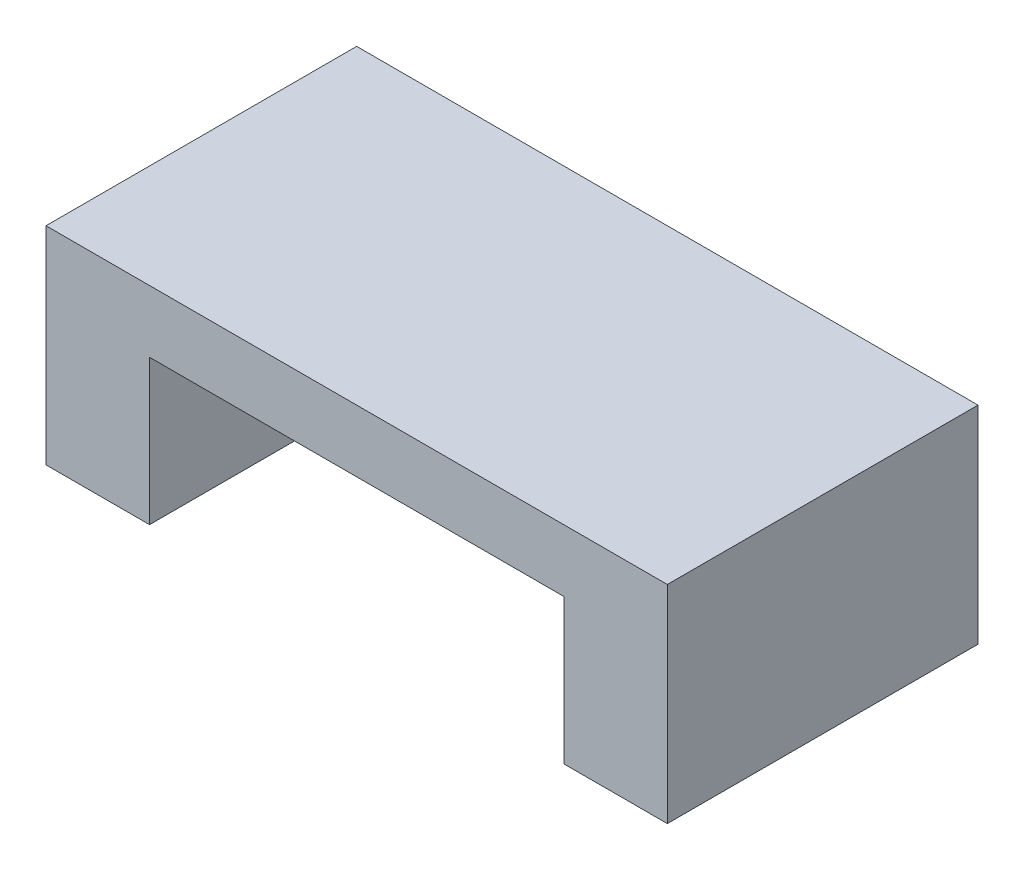
SolidWorks part; units mm, degrees
ref_plane "Front Plane" through (0, 0, 0) normal (0, 0, 1) x (1, 0, 0)
ref_plane "Top Plane" through (0, 0, 0) normal (0, 1, 0) x (1, 0, 0)
ref_plane "Right Plane" through (0, 0, 0) normal (1, 0, 0) x (0, 0, -1)
sketch "Sketch3" plane through (0, 0, 0) normal (0, 1, 0) x (1, 0, 0)
  line L1 (-15, -7.5) -> (15, -7.5)
  line L2 (-15, -7.5) -> (-15, 7.5)
  line L3 (-15, 7.5) -> (15, 7.5)
  line L4 (15, -7.5) -> (15, 7.5)
  line L5 (-15, -7.5) -> (15, 7.5) construction
  line L6 (-15, 7.5) -> (15, -7.5) construction
  point P0 (0, 0)
  dimension "D1" = 30
  dimension "D2" = 15
extrude "Boss-Extrude1" add sketch "Sketch3" along normal blind 10
sketch "Sketch4" plane through (0, 0, 7.5) normal (0, 0, 1) x (1, 0, 0)
  line L0 (-15, 0) -> (15, 0) construction
  line L1 (-10, 0) -> (10, 0)
  line L2 (-10, 0) -> (-10, 7)
  line L3 (-10, 7) -> (10, 7)
  line L4 (10, 0) -> (10, 7)
  line L5 (-15, 10) -> (-15, 0) construction
  line L6 (15, 10) -> (15, 0) construction
  dimension "D1" = 7
  dimension "D2" = 5
  dimension "D3" = 5
extrude "Cut-Extrude1" cut sketch "Sketch4" against normal through all
sketch "Sketch5" plane through (0, 0, 0) normal (0, -1, 0) x (1, 0, 0)
  line L0 (10, -7.5) -> (10, 7.5) construction
  line L1 (10, 7.5) -> (15, 7.5) construction
  line L2 (-10, -7.5) -> (-10, 7.5) construction
  line L3 (-15, 7.5) -> (-10, 7.5) construction
  circle A0 centre (12.5, 0) radius 1.5
  circle A1 centre (-12.5, 0) radius 1.5
  point P10 (0, 0)
  dimension "D1" = 2.5
  dimension "D3" = 2.5
  dimension "D2" = 7.5
  dimension "D4" = 7.5
extrude "Cut-Extrude2" cut sketch "Sketch5" against normal blind 5
